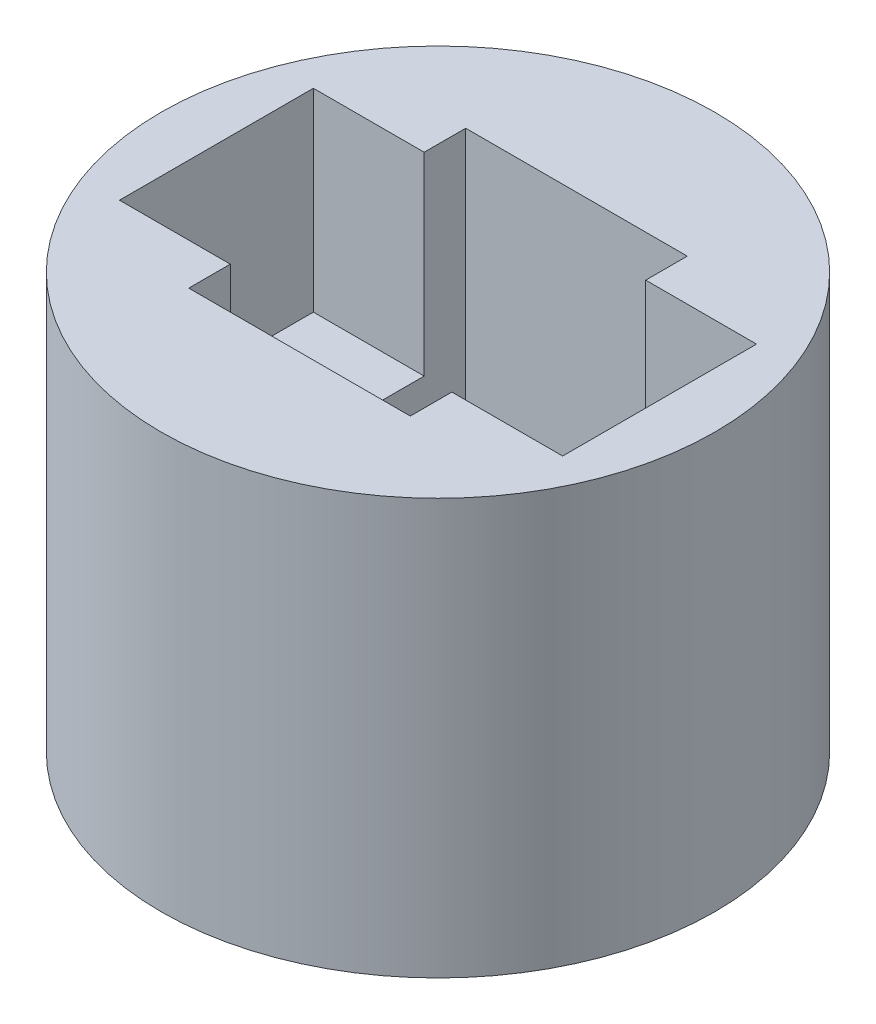
SolidWorks part; units mm, degrees
ref_plane "Alzado" through (0, 0, 0) normal (0, 0, 1) x (1, 0, 0)
ref_plane "Planta" through (0, 0, 0) normal (0, 1, 0) x (1, 0, 0)
ref_plane "Vista lateral" through (0, 0, 0) normal (1, 0, 0) x (0, 0, -1)
sketch "Croquis1" plane through (0, 0, 0) normal (0, 0, 1) x (1, 0, 0)
  line L1 (0, 0) -> (5, 0)
  line L2 (0, 0) -> (0, 7.5)
  line L3 (0, 7.5) -> (5, 7.5)
  line L4 (5, 0) -> (5, 7.5)
  dimension "D1" = 5
  dimension "D2" = 7.5
revolve "Revolución1" add sketch "Croquis1" angle 360 about L2
sketch "Croquis2" plane through (0, 7.5, 0) normal (0, 1, 0) x (1, 0, 0)
  line L0 (-3, 0.5) -> (3, 0.5)
  line L1 (-2, -2.5) -> (2, -2.5)
  line L2 (-2, -2.5) -> (-2, 2.5)
  line L3 (-2, 2.5) -> (2, 2.5)
  line L4 (2, -2.5) -> (2, 2.5)
  line L5 (-2, -2.5) -> (2, 2.5) construction
  line L6 (-2, 2.5) -> (2, -2.5) construction
  line L7 (-3, -0.5) -> (3, -0.5)
  circle A0 centre (3, 0) radius 0.5
  circle A1 centre (-3, 0) radius 0.5
  point P0 (0, 0)
  point P13 (0, 0)
  dimension "D3" = 1
  dimension "D1" = 4
  dimension "D2" = 5
  dimension "D4" = 3
  dimension "D6" = 3
  dimension "D5" = 2
extrude "Cortar-Extruir1" cut sketch "Croquis2" against normal through all contours A1 | A1 L7 L2 L0 | L2 L7 L4 L0 | L0 L4 L3 L2 | L7 L2 L1 L4 | A0 L0 L4 L7 | A0
sketch "Croquis3" plane through (0, 7.5, 0) normal (0, 1, 0) x (1, 0, 0)
  line L1 (-4, -1.75) -> (4, -1.75)
  line L2 (-4, -1.75) -> (-4, 1.75)
  line L3 (-4, 1.75) -> (4, 1.75)
  line L4 (4, -1.75) -> (4, 1.75)
  line L5 (-4, -1.75) -> (4, 1.75) construction
  line L6 (-4, 1.75) -> (4, -1.75) construction
  point P0 (0, 0)
  dimension "D1" = 8
  dimension "D2" = 3.5
extrude "Cortar-Extruir2" cut sketch "Croquis3" against normal blind 3.5
